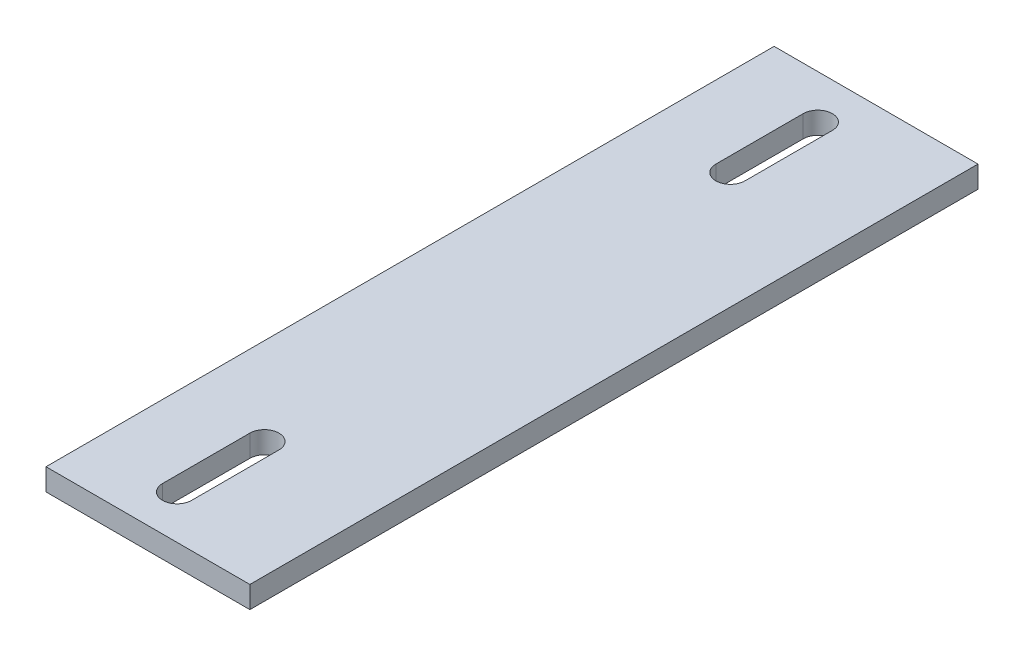
SolidWorks part; units mm, degrees
material "ASTM A36 Steel"
ref_plane "Front Plane" through (0, 0, 0) normal (0, 0, 1) x (1, 0, 0)
ref_plane "Top Plane" through (0, 0, 0) normal (0, 1, 0) x (1, 0, 0)
ref_plane "Right Plane" through (0, 0, 0) normal (1, 0, 0) x (0, 0, -1)
sketch "Sketch1" plane through (0, 0, 0) normal (0, 1, 0) x (1, 0, 0)
  line L1 (22.225, 79.375) -> (-22.225, 79.375)
  line L2 (22.225, 79.375) -> (22.225, -79.375)
  line L3 (22.225, -79.375) -> (-22.225, -79.375)
  line L4 (-22.225, 79.375) -> (-22.225, -79.375)
  line L5 (22.225, 79.375) -> (-22.225, -79.375) construction
  line L6 (22.225, -79.375) -> (-22.225, 79.375) construction
  point P0 (0, 0)
  dimension "D1" = 158.75
  dimension "D2" = 44.45
extrude "Boss-Extrude1" add sketch "Sketch1" along normal blind 4.7625
sketch "Sketch2" plane through (0, 4.7625, 0) normal (0, 1, 0) x (1, 0, 0)
  line L0 (-22.225, 79.375) -> (-22.225, -79.375) construction
  line L3 (3.175, -60.325) -> (-3.175, -60.325) construction
  line L6 (3.175, -60.325) -> (3.175, 60.325) construction
  line L7 (3.175, 60.325) -> (-3.175, 60.325) construction
  line L8 (-3.175, -60.325) -> (-3.175, 60.325) construction
  line L9 (3.175, -60.325) -> (-3.175, 60.325) construction
  line L10 (3.175, 60.325) -> (-3.175, -60.325) construction
  line L11 (-22.225, -79.375) -> (22.225, -79.375) construction
  line L12 (-3.175, -50.8) -> (-3.175, -69.85) construction
  line L13 (0, -50.8) -> (0, -69.85)
  line L14 (-6.35, -50.8) -> (-6.35, -69.85)
  line L15 (-3.175, 50.8) -> (-3.175, 69.85) construction
  line L16 (-6.35, 50.8) -> (-6.35, 69.85)
  line L17 (0, 50.8) -> (0, 69.85)
  line L18 (3.175, -50.8) -> (3.175, -69.85) construction
  line L19 (6.35, -50.8) -> (6.35, -69.85)
  line L20 (0, -50.8) -> (0, -69.85)
  line L21 (3.175, 69.85) -> (3.175, 50.8) construction
  line L22 (6.35, 69.85) -> (6.35, 50.8)
  line L23 (0, 69.85) -> (0, 50.8)
  arc A0 (0, -50.8) -> (-6.35, -50.8) centre (-3.175, -50.8) ccw
  arc A1 (-6.35, -69.85) -> (0, -69.85) centre (-3.175, -69.85) ccw
  arc A2 (-6.35, 50.8) -> (0, 50.8) centre (-3.175, 50.8) ccw
  arc A3 (0, 69.85) -> (-6.35, 69.85) centre (-3.175, 69.85) ccw
  arc A4 (6.35, -50.8) -> (0, -50.8) centre (3.175, -50.8) ccw
  arc A5 (0, -69.85) -> (6.35, -69.85) centre (3.175, -69.85) ccw
  arc A6 (6.35, 69.85) -> (0, 69.85) centre (3.175, 69.85) ccw
  arc A7 (0, 50.8) -> (6.35, 50.8) centre (3.175, 50.8) ccw
  point P0 (0, 0)
  point P11 (-3.175, -60.325)
  point P18 (-3.175, 60.325)
  point P27 (3.175, -60.325)
  point P34 (3.175, 60.325)
  dimension "D1" = 19.05
  dimension "D2" = 19.05
  dimension "D3" = 19.05
  dimension "D4" = 6.35
extrude "Cut-Extrude1" cut sketch "Sketch2" against normal through all contours L17 A3 L16 A2 | L14 A1 L13 A0
